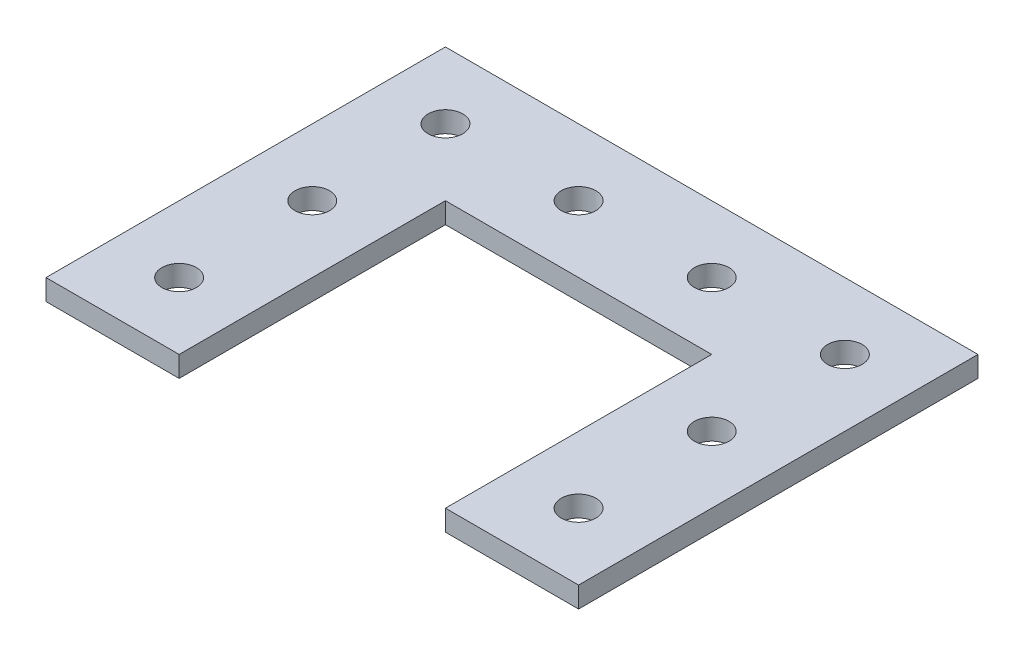
SolidWorks part; units mm, degrees
ref_plane "Front Plane" through (0, 0, 0) normal (0, 0, 1) x (1, 0, 0)
ref_plane "Top Plane" through (0, 0, 0) normal (0, 1, 0) x (1, 0, 0)
ref_plane "Right Plane" through (0, 0, 0) normal (1, 0, 0) x (0, 0, -1)
sketch "Sketch1" plane through (0, 0, 0) normal (0, 1, 0) x (1, 0, 0)
  line L0 (0, 0) -> (0, 60)
  line L1 (0, 60) -> (80, 60)
  line L2 (80, 60) -> (80, 0)
  line L3 (80, 0) -> (60, 0)
  line L4 (60, 0) -> (60, 40)
  line L5 (60, 40) -> (20, 40)
  line L6 (20, 40) -> (20, 0)
  line L7 (20, 0) -> (0, 0)
  circle A0 centre (10, 50) radius 2.6
  circle A1 centre (10, 30) radius 2.6
  circle A2 centre (10, 10) radius 2.6
  circle A3 centre (30, 50) radius 2.6
  circle A4 centre (50, 50) radius 2.6
  circle A5 centre (70, 50) radius 2.6
  circle A6 centre (70, 30) radius 2.6
  circle A7 centre (70, 10) radius 2.6
  dimension "D7" = 20
  dimension "D11" = 20
  dimension "D16" = 5.2
  dimension "D14" = 10
  dimension "D15" = 10
  dimension "D1" = 60
  dimension "D2" = 20
  dimension "D3" = 20
  dimension "D4" = 60
  dimension "D5" = 20
  dimension "D6" = 80
  dimension "D8" = 20
  dimension "D9" = 20
  dimension "D10" = 20
  dimension "D12" = 20
  dimension "D13" = 20
extrude "Boss-Extrude1" add sketch "Sketch1" along normal blind 3.125
